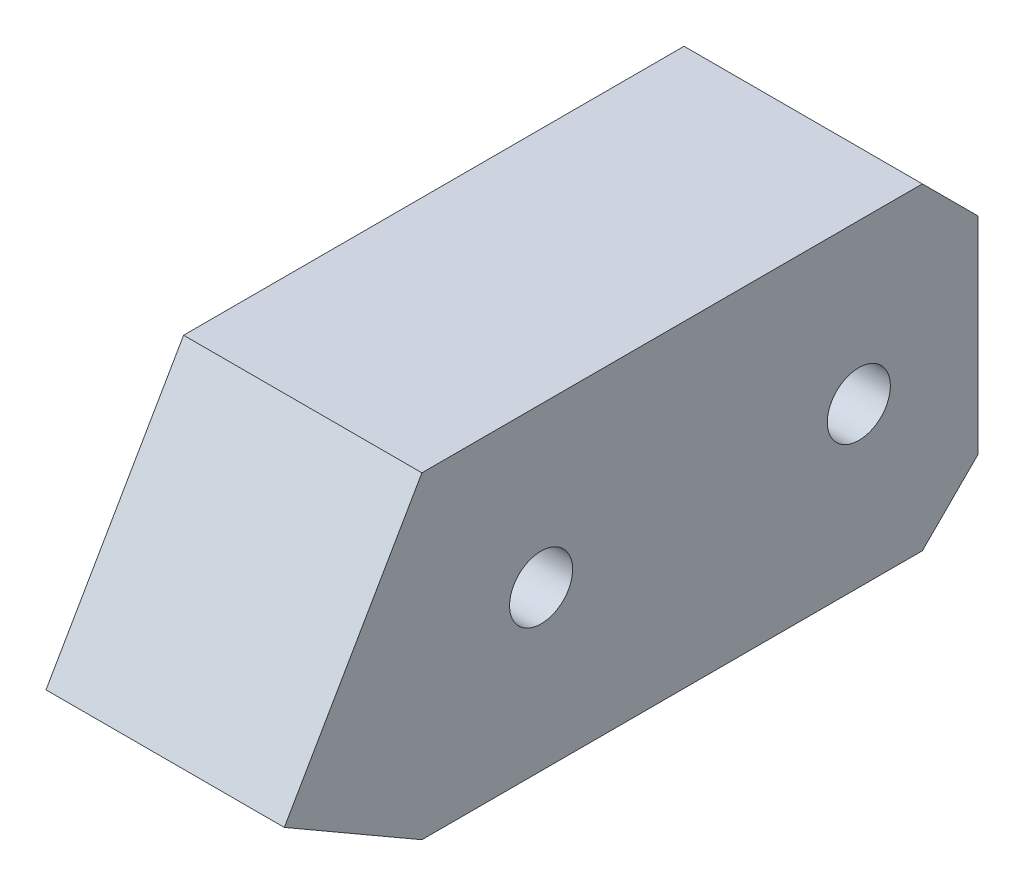
SolidWorks part; units mm, degrees
material "ABS"
ref_plane "Plano frontal" through (0, 0, 0) normal (0, 0, 1) x (1, 0, 0)
ref_plane "Plano superior" through (0, 0, 0) normal (0, 1, 0) x (1, 0, 0)
ref_plane "Plano direito" through (0, 0, 0) normal (1, 0, 0) x (0, 0, -1)
sketch "Esboço1" plane through (0, 0, 0) normal (1, 0, 0) x (0, 0, -1)
  line L0 (-35, 0) -> (-20, 0) construction
  line L1 (35, 20) -> (-35, 20)
  line L2 (35, 20) -> (35, -20)
  line L3 (35, -20) -> (-35, -20)
  line L5 (35, 20) -> (-35, -20) construction
  line L6 (35, -20) -> (-35, 20) construction
  line L7 (-20, 0) -> (20, 0) construction
  line L8 (20, 0) -> (35, 0) construction
  line L10 (-52.3205, -10) -> (-35, -20)
  line L11 (-35, -20) -> (-35, 20) construction
  line L12 (-35, 20) -> (-52.3205, -10)
  circle A0 centre (-20, 0) radius 3.97
  circle A1 centre (20, 0) radius 3.97
  point P0 (0, 0)
  dimension "D4" = 7.94
  dimension "D1" = 40
  dimension "D2" = 70
  dimension "D3" = 40
  dimension "D5" = 60
  dimension "D6" = 30
extrude "Ressalto-extrusão1" add sketch "Esboço1" along normal mid plane 30
sketch "Esboço2" plane through (0, -20, 0) normal (0, -1, 0) x (1, 0, 0)
  line L0 (0, 35) -> (0, 20) construction
  line L1 (15, 35) -> (-15, 35) construction
  line L2 (0, 20) -> (0, -20) construction
  line L3 (0, -20) -> (0, -35) construction
  line L4 (15, -35) -> (-15, -35) construction
  circle A0 centre (0, 20) radius 3.97
  circle A1 centre (0, -20) radius 3.97
  dimension "D2" = 7.94
  dimension "D1" = 40
extrude "Corte-extrusão2" cut sketch "Esboço2" against normal blind 20
chamfer "Chanfro1" distance 7 angle 45 2 edges at (0, -20, -35) (0, 20, -35)
sketch "Esboço4" plane through (0, -30.1554, 17.4103) normal (0, -0.866, 0.5) x (1, 0, 0)
  line L0 (-15, 30.3109) -> (15, 30.3109) construction
  line L1 (-15, 40.3109) -> (-15, 20.3109) construction
  line L2 (15, 40.3109) -> (15, 20.3109) construction
  line L3 (0, 20.3109) -> (0, 30.3109) construction
  line L4 (15, 20.3109) -> (-15, 20.3109) construction
  circle A0 centre (0, 30.3109) radius 3.97
  dimension "D1" = 7.94
extrude "Corte-extrusão4" cut sketch "Esboço4" against normal blind 20
